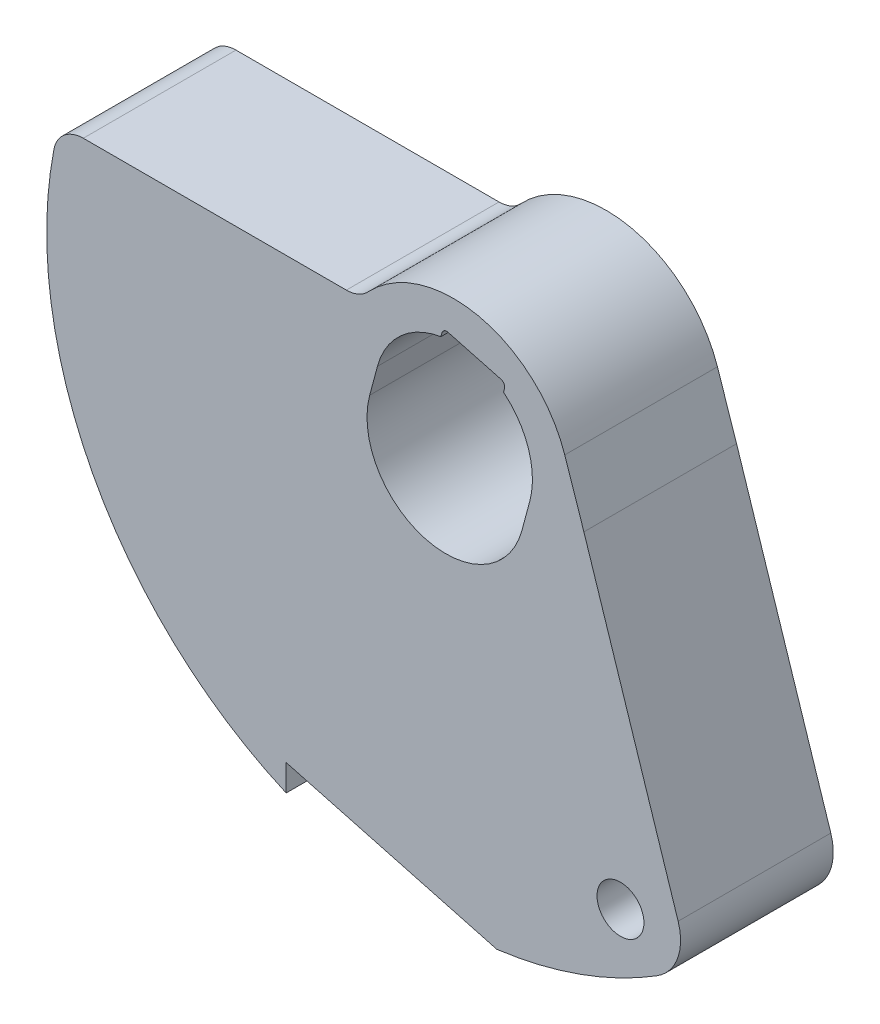
SolidWorks part; units mm, degrees
material "Cast Stainless Steel"
ref_plane "Front Plane" through (0, 0, 0) normal (0, 0, 1) x (1, 0, 0)
ref_plane "Top Plane" through (0, 0, 0) normal (0, 1, 0) x (1, 0, 0)
ref_plane "Right Plane" through (0, 0, 0) normal (1, 0, 0) x (0, 0, -1)
sketch "Sketch1" plane through (0, 0, 0) normal (0, 0, 1) x (1, 0, 0)
  line L0 (0, 40.7088) -> (0, -42.4788) construction
  line L1 (50.0011, 0) -> (-47.9361, 0) construction
  line L2 (0, 0) -> (4.815, 17.9697) construction
  line L3 (-7.4706, 2.0017) -> (6.4814, -1.7367) construction
  line L4 (-7.0762, 3.4738) -> (6.8758, -0.2646) construction
  line L5 (-3.8765, 1.0387) -> (-3.482, 2.5108)
  line L6 (4.2709, 0.4334) -> (3.8765, -1.0387)
  line L7 (-5.0653, 5.08) -> (-18.4566, 5.08)
  line L8 (6.0531, 3.3717) -> (7.0281, 0.4672)
  line L9 (12.9403, -3.6173) -> (17.147, -10.9034)
  line L10 (0, 0) -> (5.8427, -10.1199) construction
  line L11 (0, 0) -> (43.883, -11.7584) construction
  line L12 (8.89, 40.7088) -> (8.89, -42.4788) construction
  line L13 (50.0011, -15.24) -> (-47.9361, -15.24) construction
  line L14 (-1.0387, -3.8765) -> (-9.0244, -1.7367) construction
  line L15 (-8.128, -17.2812) -> (-8.128, -18.6236)
  line L16 (-8.128, -17.2812) -> (2.5931, -20.1539)
  line L17 (2.8088, 5.0851) -> (0.11, 5.8082)
  line L18 (1.4594, 5.4467) -> (-6.5263, 7.5864) construction
  line L21 (2.9359, 4.578) -> (2.9884, 4.774)
  line L24 (-0.2536, 5.4326) -> (-0.2011, 5.6286)
  arc A0 (-3.8765, 1.0387) -> (3.8765, -1.0387) centre (0, 0) ccw
  arc A1 (6.1601, -0.0728) -> (6.1791, 0) centre (0.3944, 1.4721) ccw
  arc A2 (4.2709, 0.4334) -> (2.9359, 4.578) centre (0.3944, 1.4721) ccw
  arc A3 (7.0281, 0.4672) -> (12.6001, -3.4269) centre (12.446, 2.286) ccw
  arc A4 (6.0531, 3.3717) -> (-3.9548, 5.5602) centre (0.3944, 1.4721) ccw
  arc A5 (-19.953, 3.8443) -> (-8.128, -18.6236) centre (0, 0) ccw
  arc A6 (12.6001, -3.4269) -> (12.9403, -3.6173) centre (12.6104, -3.8078) cw
  arc A7 (2.5931, -20.1539) -> (17.147, -10.9034) centre (0, 0) ccw
  arc A8 (-18.4566, 5.08) -> (-19.953, 3.8443) centre (-18.4566, 3.556) ccw
  arc A9 (-5.0653, 5.08) -> (-3.9548, 5.5602) centre (-5.0653, 6.604) ccw
  circle A10 centre (8.89, -15.24) radius 1.1938
  arc A11 (-0.2536, 5.4326) -> (-3.482, 2.5108) centre (0.3944, 1.4721) ccw
  arc A12 (2.8088, 5.0851) -> (2.9884, 4.774) centre (2.7431, 4.8397) cw
  arc A13 (-0.2011, 5.6286) -> (0.11, 5.8082) centre (0.0443, 5.5629) cw
  point P35 (-9.9822, 40.7088)
  point P36 (-9.9822, -42.4788)
  point P48 (1.5947, -0.4273)
  point P50 (6.4097, 17.5424)
  point P51 (-1.5947, 0.4273)
  point P52 (3.2202, 18.397)
  dimension "D1" = 8.0264
  dimension "D4" = 11.938
  dimension "D6" = 11.43
  dimension "D11" = 40.64
  dimension "D12" = 0.381
  dimension "D16" = 1.524
  dimension "D17" = 1.524
  dimension "D20" = 2.3876
  dimension "D24" = 0.254
  dimension "D2" = 15
  dimension "D5" = 5.08
  dimension "D7" = 2.286
  dimension "D8" = 12.446
  dimension "D9" = 60
  dimension "D10" = 9.398
  dimension "D13" = 15
  dimension "D14" = 18.796
  dimension "D15" = 8.128
  dimension "D22" = 3.302
  dimension "D23" = 1.651
  dimension "D3" = 1.524
  dimension "D18" = 8.89
  dimension "D19" = 15.24
  dimension "D21" = 9.652
extrude "Boss-Extrude1" add sketch "Sketch1" against normal blind 7.7724
sketch "Sketch2" plane through (0, 0, 0) normal (0, 0, 1) x (1, 0, 0)
  line L0 (7.0281, 0.4672) -> (12.4084, -16.0914)
  arc A0 (2.5931, -20.1539) -> (17.147, -10.9034) centre (0, 0) ccw construction
  dimension "D1" = 72
extrude "Cut-Extrude1" cut sketch "Sketch2" against normal through all and the other way through all
fillet "Fillet1" radius 2.54 1 edges at (12.4084, -16.0914, -3.8862)
